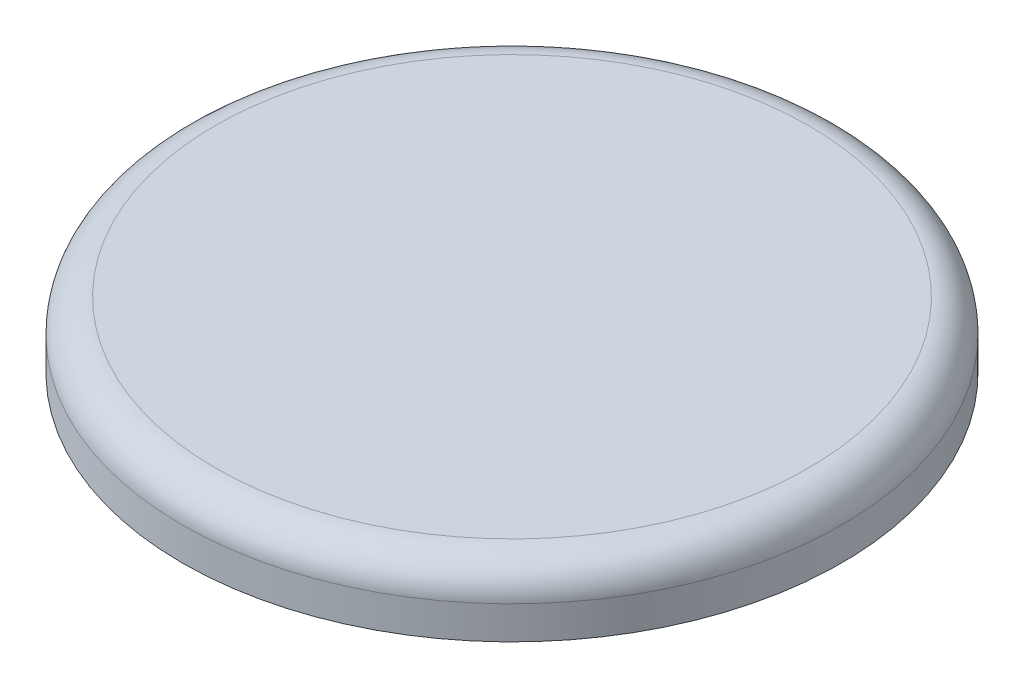
SolidWorks part; units mm, degrees
ref_plane "Front Plane" through (0, 0, 0) normal (0, 0, 1) x (1, 0, 0)
ref_plane "Top Plane" through (0, 0, 0) normal (0, 1, 0) x (1, 0, 0)
ref_plane "Right Plane" through (0, 0, 0) normal (1, 0, 0) x (0, 0, -1)
sketch "Sketch1" plane through (0, 0, 0) normal (0, 1, 0) x (1, 0, 0)
  circle A0 centre (0, 0) radius 10
extrude "Boss-Extrude1" add sketch "Sketch1" along normal blind 2
fillet "Fillet1" radius 1 1 edges at (0, 2, 10)
